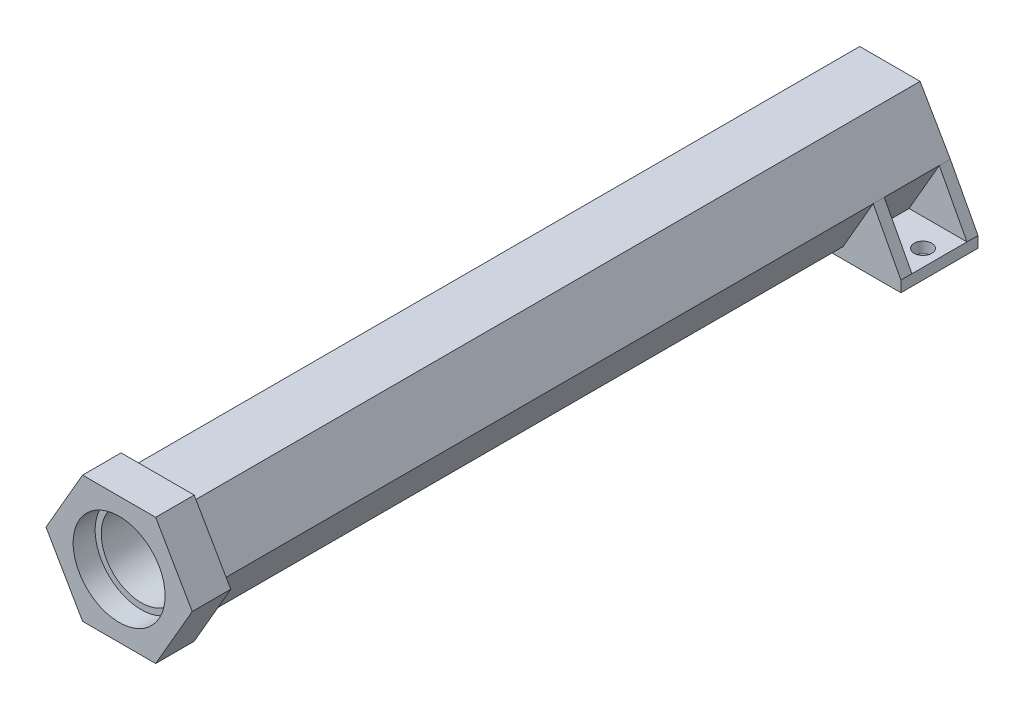
SolidWorks part; units mm, degrees
material "ABS"
ref_plane "Ebene vorne" through (0, 0, 0) normal (0, 0, 1) x (1, 0, 0)
ref_plane "Ebene oben" through (0, 0, 0) normal (0, 1, 0) x (1, 0, 0)
ref_plane "Ebene rechts" through (0, 0, 0) normal (1, 0, 0) x (0, 0, -1)
sketch "Skizze1" plane through (0, 0, 0) normal (0, 0, 1) x (1, 0, 0)
  line L1 (-10.9697, 0) -> (-5.4848, -9.5)
  line L2 (-5.4848, -9.5) -> (5.4848, -9.5)
  line L6 (5.4848, -9.5) -> (10.9697, 0)
  line L7 (10.9697, 0) -> (5.4848, 9.5)
  line L8 (5.4848, 9.5) -> (-5.4848, 9.5)
  line L9 (-5.4848, 9.5) -> (-10.9697, 0)
  circle A0 centre (0, 0) radius 7.25
  circle A1 centre (0, 0) radius 9.5 construction
  dimension "D3" = 14.5
  dimension "D4" = 19
extrude "Aufsatz-Linear austragen1" add sketch "Skizze1" along normal blind 136
sketch "Skizze2" plane through (0, 0, 0) normal (0, 0, 1) x (1, 0, 0)
  circle A0 centre (0, 0) radius 7.25
  circle A4 centre (0, 0) radius 7.25 construction
extrude "Aufsatz-Linear austragen2" add sketch "Skizze2" along normal blind 2
sketch3d "3D-Skizze5" plane through (0, 0, 0) normal (0, 0, 1) x (1, 0, 0)
  dimension "D1" = 133
sketch "Skizze3" plane through (0, 0, 133) normal (0, 0, 1) x (1, 0, 0)
  line L0 (-5.4848, -9.5) -> (5.4848, -9.5) construction
  line L1 (13.2791, 0) -> (6.6395, 11.5)
  line L2 (6.6395, 11.5) -> (-6.6395, 11.5)
  line L3 (-6.6395, 11.5) -> (-13.2791, 0)
  line L4 (-13.2791, 0) -> (-6.6395, -11.5)
  line L7 (-6.6395, -11.5) -> (6.6395, -11.5)
  line L8 (6.6395, -11.5) -> (13.2791, 0)
  circle A0 centre (0, 0) radius 8.35
  circle A1 centre (0, 0) radius 11.5 construction
  dimension "D1" = 16.7
  dimension "D2" = 2
extrude "Aufsatz-Linear austragen3" add sketch "Skizze3" along normal blind 7
sketch "Skizze7" plane through (0, 0, 0) normal (0, 0, 1) x (1, 0, 0)
  line L0 (10.9697, 0) -> (5.4848, -9.5)
  line L1 (5.4848, -9.5) -> (16, -9.5)
  line L2 (16, -9.5) -> (10.9697, 0)
  line L3 (-5.4848, -9.5) -> (-10.9697, 0)
  line L4 (-10.9697, 0) -> (-16, -9.5)
  line L5 (-16, -9.5) -> (-5.4848, -9.5)
  dimension "D1" = 32
extrude "Aufsatz-Linear austragen6" add sketch "Skizze7" along normal blind 2
pattern_linear "Lineares Muster3" count 2 spacing 12 along (0, 0, 1) of "Aufsatz-Linear austragen6"
sketch "Skizze12" plane through (0, -9.5, 0) normal (0, -1, 0) x (1, 0, 0)
  line L1 (-16, 14) -> (16, 14)
  line L2 (-16, 14) -> (-16, 0)
  line L3 (-16, 0) -> (16, 0)
  line L4 (16, 14) -> (16, 0)
  circle A0 centre (-13, 7) radius 1.6
  circle A1 centre (13, 7) radius 1.6
  dimension "D1" = 3.2
  dimension "D7" = 7
  dimension "D2" = 14
  dimension "D3" = 32
  dimension "D4" = 3
  dimension "D5" = 3
  dimension "D8" = 7
  dimension "D6" = 2
extrude "Aufsatz-Linear austragen14" add sketch "Skizze12" along normal blind 2
sketch "Skizze14" plane through (0, 0, 0) normal (0, 0, -1) x (-1, 0, 0)
  circle A0 centre (0, 0) radius 2.6
  dimension "D1" = 5.2
extrude "Schnitt-Linear austragen1" cut sketch "Skizze14" against normal up to surface (2 mm away) up to face at (7.25, 0, 2)
